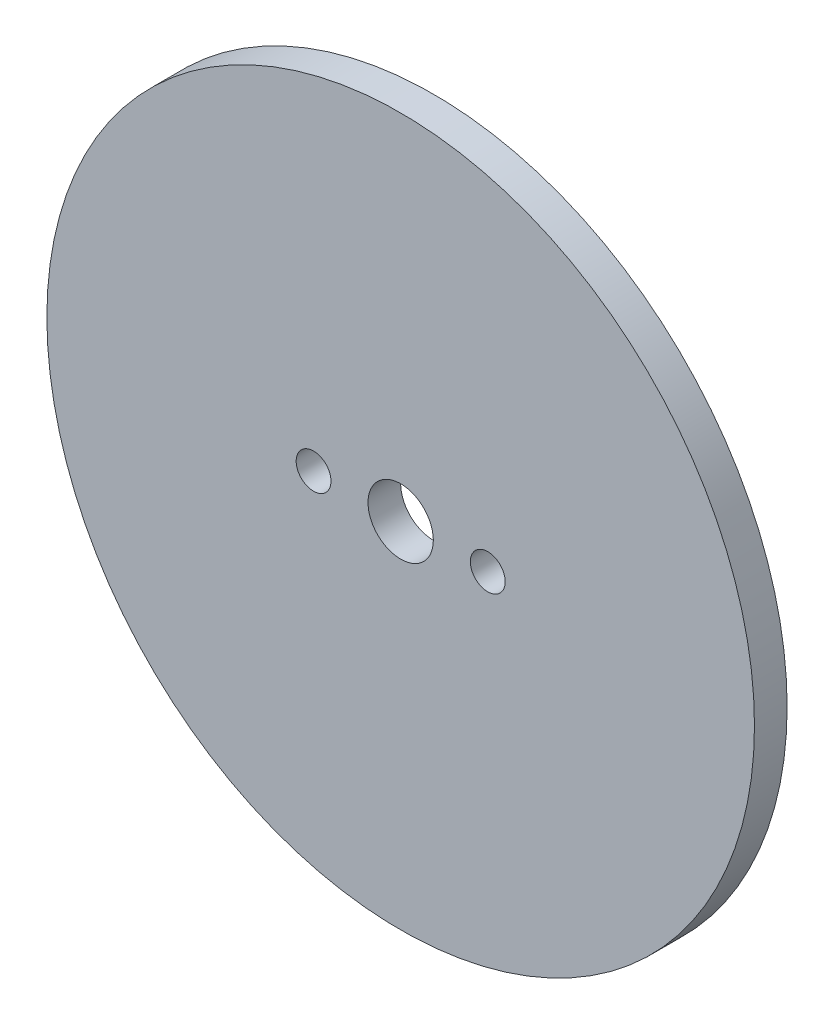
SolidWorks part; units mm, degrees
material "MDF"
ref_plane "Plano frontal" through (0, 0, 0) normal (0, 0, 1) x (1, 0, 0)
ref_plane "Plano superior" through (0, 0, 0) normal (0, 1, 0) x (1, 0, 0)
ref_plane "Plano direito" through (0, 0, 0) normal (1, 0, 0) x (0, 0, -1)
sketch "Esboço1" plane through (0, 0, 0) normal (0, 0, 1) x (1, 0, 0)
  line L0 (8, 0) -> (-8, 0) construction
  circle A0 centre (0, 0) radius 32.5
  circle A1 centre (0, 0) radius 3
  circle A2 centre (8, 0) radius 1.6
  circle A3 centre (-8, 0) radius 1.6
  dimension "D1" = 16
  dimension "D2" = 3.2
  dimension "D3" = 65
  dimension "D4" = 6
extrude "Ressalto-extrusão1" add sketch "Esboço1" along normal blind 3
